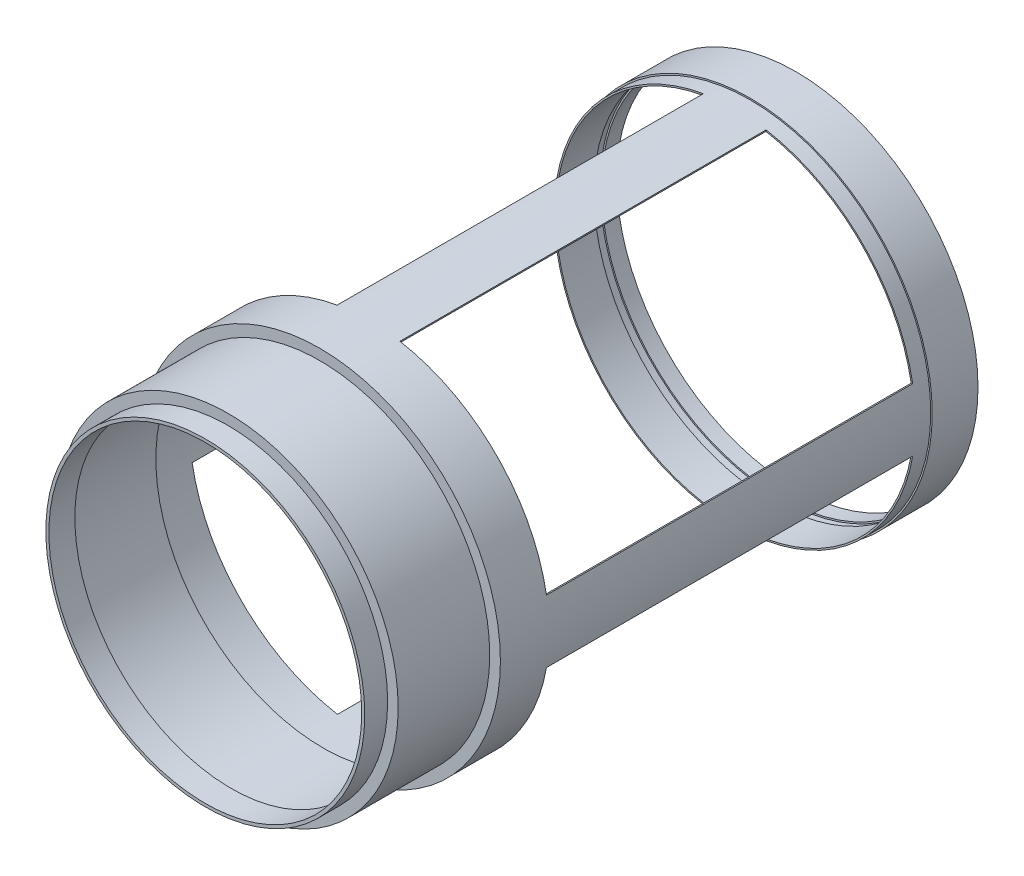
SolidWorks part; units mm, degrees
material "6063-T4"
ref_plane "Front Plane" through (0, 0, 0) normal (0, 0, 1) x (1, 0, 0)
ref_plane "Top Plane" through (0, 0, 0) normal (0, 1, 0) x (1, 0, 0)
ref_plane "Right Plane" through (0, 0, 0) normal (1, 0, 0) x (0, 0, -1)
sketch "Sketch1" plane through (0, 0, 0) normal (0, 0, 1) x (1, 0, 0)
  circle A0 centre (0, 0) radius 117.4
  circle A1 centre (0, 0) radius 119.4
extrude "Extrude1" add sketch "Sketch1" along normal blind 10
sketch "Sketch2" plane through (0, 0, 10) normal (0, 0, 1) x (1, 0, 0)
  circle A0 centre (0, 0) radius 119.4
  circle A1 centre (0, 0) radius 118.4
extrude "Extrude2" add sketch "Sketch2" along normal blind 5
sketch "Sketch3" plane through (0, 0, 15) normal (0, 0, 1) x (1, 0, 0)
  circle A0 centre (0, 0) radius 117.4
  circle A1 centre (0, 0) radius 119.4
extrude "Extrude3" add sketch "Sketch3" along normal blind 15
sketch "Sketch4" plane through (0, 0, 30) normal (0, 0, 1) x (1, 0, 0)
  circle A0 centre (0, 0) radius 117.4
  circle A1 centre (0, 0) radius 118.4
extrude "Extrude4" add sketch "Sketch4" along normal blind 10
sketch "Sketch5" plane through (0, 0, 40) normal (0, 0, 1) x (1, 0, 0)
  line L0 (0, 0) -> (151.5176, 26.7166) construction
  line L1 (0, 0) -> (150.2034, -26.4849) construction
  line L2 (0, 0) -> (25.5041, 144.6412) construction
  line L3 (0, 0) -> (-165.3286, 29.1519) construction
  line L4 (0, 0) -> (-25.9286, -147.0486) construction
  line L5 (0, 0) -> (-30.0243, 170.2763) construction
  line L6 (0, 0) -> (-142.6795, -25.1582) construction
  line L7 (0, 0) -> (26.4406, -149.9522) construction
  line L8 (20.5599, 116.6012) -> (20.3863, 115.6164)
  line L9 (-20.5599, 116.6012) -> (-20.3863, 115.6164)
  line L10 (116.6012, 20.5599) -> (115.6164, 20.3863)
  line L11 (116.6012, -20.5599) -> (115.6164, -20.3863)
  line L12 (20.5599, -116.6012) -> (20.3863, -115.6164)
  line L13 (-20.5599, -116.6012) -> (-20.3863, -115.6164)
  line L14 (-115.6164, -20.3863) -> (-116.6012, -20.5599)
  line L15 (-115.6164, 20.3863) -> (-116.6012, 20.5599)
  arc A0 (116.6012, 20.5599) -> (116.6012, -20.5599) centre (0, 0) cw
  circle A1 centre (0, 0) radius 118.4 construction
  arc A2 (115.6164, 20.3863) -> (115.6164, -20.3863) centre (0, 0) cw
  circle A3 centre (0, 0) radius 117.4 construction
  arc A4 (20.5599, -116.6012) -> (-20.5599, -116.6012) centre (0, 0) cw
  arc A5 (20.3863, -115.6164) -> (-20.3863, -115.6164) centre (0, 0) cw
  arc A6 (-115.6164, -20.3863) -> (-115.6164, 20.3863) centre (0, 0) cw
  arc A7 (-116.6012, -20.5599) -> (-116.6012, 20.5599) centre (0, 0) cw
  arc A8 (-20.5599, 116.6012) -> (20.5599, 116.6012) centre (0, 0) cw
  arc A9 (-20.3863, 115.6164) -> (20.3863, 115.6164) centre (0, 0) cw
extrude "Extrude5" add sketch "Sketch5" along normal blind 240
sketch "Sketch6" plane through (0, 0, 280) normal (0, 0, 1) x (1, 0, 0)
  circle A0 centre (0, 0) radius 118.4
  circle A1 centre (0, 0) radius 117.4
extrude "Extrude6" add sketch "Sketch6" along normal blind 30
sketch "Sketch7" plane through (0, 0, 310) normal (0, 0, 1) x (1, 0, 0)
  circle A0 centre (0, 0) radius 118.4
  circle A1 centre (0, 0) radius 109.4
extrude "Extrude7" add sketch "Sketch7" along normal blind 2
sketch "Sketch8" plane through (0, 0, 312) normal (0, 0, 1) x (1, 0, 0)
  circle A0 centre (0, 0) radius 109.4
  circle A1 centre (0, 0) radius 111.4
extrude "Extrude8" add sketch "Sketch8" along normal blind 60
sketch "Sketch9" plane through (0, 0, 372) normal (0, 0, 1) x (1, 0, 0)
  circle A0 centre (0, 0) radius 102.5
  circle A1 centre (0, 0) radius 111.4
extrude "Extrude9" add sketch "Sketch9" against normal blind 2
sketch "Sketch10" plane through (0, 0, 372) normal (0, 0, 1) x (1, 0, 0)
  circle A0 centre (0, 0) radius 102.5
  circle A1 centre (0, 0) radius 104.5
extrude "Extrude10" add sketch "Sketch10" along normal blind 15
